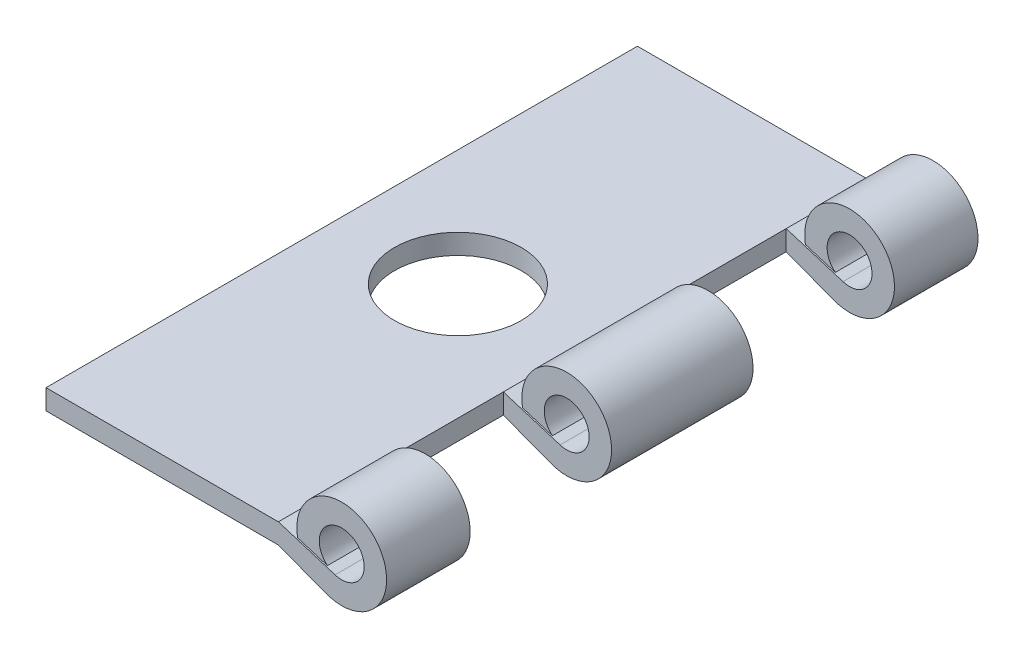
SolidWorks part; units mm, degrees
ref_plane "Front Plane" through (0, 0, 0) normal (0, 0, 1) x (1, 0, 0)
ref_plane "Top Plane" through (0, 0, 0) normal (0, 1, 0) x (1, 0, 0)
ref_plane "Right Plane" through (0, 0, 0) normal (1, 0, 0) x (0, 0, -1)
sketch "Sketch1" plane through (0, 0, 0) normal (0, 0, 1) x (1, 0, 0)
  line L0 (9.3266, -3.6068) -> (16.4617, -6.3094)
  line L1 (-25.5984, -0.5842) -> (9.3266, -0.5842)
  line L2 (9.3266, -0.5842) -> (17.8545, -3.2227)
  line L3 (-25.5984, -3.6068) -> (9.3266, -3.6068)
  line L4 (-25.5984, -0.5842) -> (-25.5984, -3.6068)
  line L5 (12.2144, -1.2118) -> (16.7027, -2.6005)
  arc A0 (17.8545, -3.2227) -> (16.7027, -2.6005) centre (18.8516, 0) ccw
  arc A1 (16.4617, -6.3094) -> (12.2144, -1.2118) centre (18.8516, 0) ccw
  circle A2 centre (18.8516, 0) radius 6.7469 construction
  circle A3 centre (18.8516, 0) radius 3.3734 construction
  dimension "D1" = 6.7469
  dimension "D4" = 13.4937
  dimension "D2" = 3.0226
  dimension "D3" = 44.45
  dimension "D5" = 34.925
  dimension "D6" = 0.5842
  dimension "D7" = 0.254
extrude "Boss-Extrude1" add sketch "Sketch1" along normal blind 88.9
sketch "Sketch2" plane through (0, -0.5842, 0) normal (0, 1, 0) x (1, 0, 0)
  line L0 (9.3266, -76.3397) -> (25.5984, -76.3397)
  line L1 (25.5984, -44.45) -> (-25.5984, -44.45) construction
  line L2 (25.5984, -76.3397) -> (25.5984, -55.0799)
  line L3 (25.5984, -55.0799) -> (9.3266, -55.0799)
  line L4 (9.3266, -12.5603) -> (25.5984, -12.5603)
  line L5 (9.3266, -55.0799) -> (9.3266, -76.3397)
  line L6 (9.3266, -33.8201) -> (9.3266, -12.5603)
  line L7 (25.5984, -33.8201) -> (9.3266, -33.8201)
  line L8 (25.5984, -12.5603) -> (25.5984, -33.8201)
  line L9 (25.5984, -33.8201) -> (25.5984, -55.0799) construction
  line L10 (-25.5984, -88.9) -> (-25.5984, 0) construction
  point P10 (-25.5984, -44.45)
  dimension "D1" = 21.2598
extrude "Cut-Extrude1" cut sketch "Sketch2" against normal mid plane 88.9
sketch "Sketch3" plane through (0, -3.6068, 0) normal (0, -1, 0) x (1, 0, 0)
  line L0 (9.3266, 44.45) -> (-25.5984, 44.45) construction
  line L1 (9.3266, 55.0799) -> (9.3266, 33.8201) construction
  line L2 (-25.5984, 88.9) -> (-25.5984, 0) construction
  circle A0 centre (-8.1359, 44.45) radius 9.525
  dimension "D1" = 19.05
extrude "Cut-Extrude2" cut sketch "Sketch3" against normal blind 88.9
